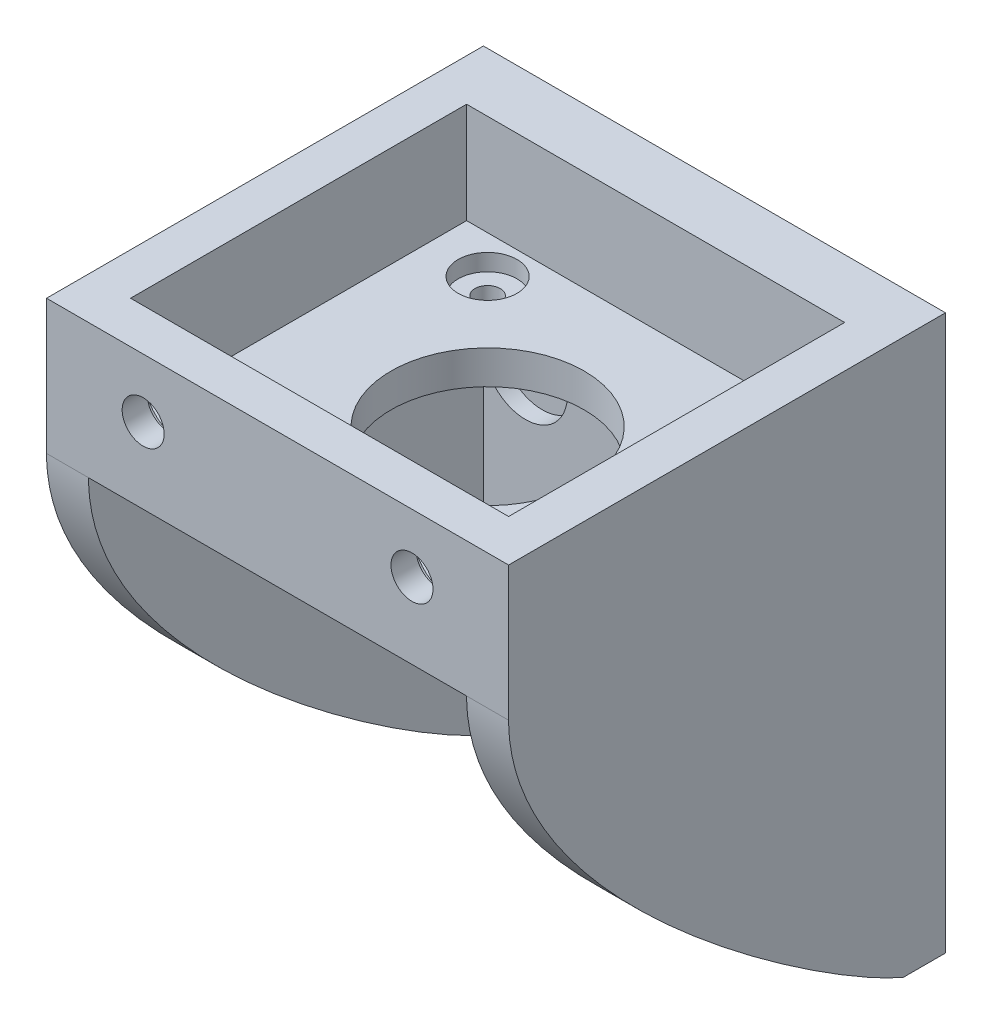
SolidWorks part; units mm, degrees
ref_plane "Front" through (0, 0, 0) normal (0, 0, 1) x (1, 0, 0)
ref_plane "Top" through (0, 0, 0) normal (0, 1, 0) x (1, 0, 0)
ref_plane "Right" through (0, 0, 0) normal (1, 0, 0) x (0, 0, -1)
sketch "Sketch1" plane through (0, 0, 0) normal (0, 0, 1) x (1, 0, 0)
  line L0 (0, 10.6846) -> (0, -12.6556) construction
  line L1 (-27.5, 25) -> (27.5, 25)
  line L2 (-27.5, 25) -> (-27.5, -25)
  line L3 (-27.5, -25) -> (27.5, -25)
  line L4 (27.5, 25) -> (27.5, -25)
  line L5 (-27.5, 25) -> (27.5, -25) construction
  line L6 (-27.5, -25) -> (27.5, 25) construction
  line L7 (-31.8369, 0) -> (16.1153, 0) construction
  circle A0 centre (-17.5, -15) radius 2.5
  circle A1 centre (17.5, -15) radius 2.5
  circle A2 centre (-17.5, 15) radius 2.5
  circle A3 centre (17.5, 15) radius 2.5
  point P0 (0, 0)
  dimension "D3" = 5
  dimension "D1" = 50
  dimension "D2" = 55
  dimension "D4" = 10
  dimension "D5" = 10
extrude "Boss-Extrude1" add sketch "Sketch1" along normal blind 5
sketch "Sketch2" plane through (0, 0, 5) normal (0, 0, 1) x (1, 0, 0)
  line L0 (-30.4627, 0) -> (10.8931, 0) construction
  circle A0 centre (-17.5, -15) radius 5
  circle A1 centre (17.5, -15) radius 5
  circle A3 centre (-17.5, 15) radius 5
  circle A4 centre (17.5, 15) radius 5
  dimension "D1" = 10
extrude "Cut-Extrude1" cut sketch "Sketch2" against normal blind 2
sketch "Sketch3" plane through (0, 25, 0) normal (0, 1, 0) x (1, 0, 0)
  line L1 (-27.5, 0) -> (27.5, 0)
  line L2 (-27.5, 0) -> (-27.5, -52)
  line L3 (-27.5, -52) -> (27.5, -52)
  line L4 (27.5, 0) -> (27.5, -52)
  dimension "D1" = 52
extrude "Boss-Extrude2" add sketch "Sketch3" along normal blind 16
sketch "Sketch4" plane through (0, 25, 0) normal (0, -1, 0) x (-1, 0, 0)
  line L0 (27.5, -5) -> (-27.5, -5) construction
  circle A0 centre (0, -27) radius 11.5
  circle A2 centre (15.5, -42.5) radius 1.5
  circle A3 centre (-15.5, -42.5) radius 1.5
  circle A4 centre (-15.5, -11.5) radius 1.5
  circle A5 centre (15.5, -11.5) radius 1.5
  dimension "D1" = 22
  dimension "D2" = 23
  dimension "D5" = 4
extrude "Cut-Extrude2" cut sketch "Sketch4" against normal through all
sketch "Sketch5" plane through (-27.5, 0, 0) normal (-1, 0, 0) x (0, 0, 1)
  line L0 (5, -25) -> (5, 25)
  line L1 (5, 25) -> (52, 25)
  spline S0 degree 3 poles (52, 25) (52, 4.233) (15.2666, -20.7199) (5, -25) knots 0 0 0 0 0.911488 0.911488 0.911488 0.911488
extrude "Boss-Extrude3" add sketch "Sketch5" against normal blind 5
mirror "Mirror1" about plane through (0, 0, 0) normal (1, 0, 0) of "Boss-Extrude3"
sketch "Sketch6" plane through (0, 41, 0) normal (0, 1, 0) x (1, 0, 0)
  line L1 (-22.5, -7) -> (22.5, -7)
  line L2 (-22.5, -7) -> (-22.5, -47)
  line L3 (-22.5, -47) -> (22.5, -47)
  line L4 (22.5, -7) -> (22.5, -47)
  line L5 (-22.5, -7) -> (22.5, -47) construction
  line L6 (-22.5, -47) -> (22.5, -7) construction
  point P0 (0, -27)
  dimension "D1" = 40
  dimension "D2" = 45
extrude "Cut-Extrude3" cut sketch "Sketch6" against normal blind 12
sketch "Sketch7" plane through (0, 29, 0) normal (0, 1, 0) x (1, 0, 0)
  circle A0 centre (-15.5, -11.5) radius 3.5
  circle A1 centre (15.5, -11.5) radius 3.5
  circle A2 centre (15.5, -42.5) radius 3.5
  circle A3 centre (-15.5, -42.5) radius 3.5
  dimension "D1" = 4
extrude "Cut-Extrude4" cut sketch "Sketch7" against normal blind 2
sketch "Sketch8" plane through (0, 0, 52) normal (0, 0, 1) x (1, 0, 0)
  line L0 (-27.5, 41) -> (27.5, 41) construction
  line L1 (27.5, 41) -> (27.5, 25) construction
  line L2 (0, 40.3655) -> (0, 13.7518) construction
  circle A0 centre (16, 34) radius 2.5
  circle A1 centre (-16, 34) radius 2.5
  dimension "D1" = 5
  dimension "D2" = 7
  dimension "D3" = 11.5
extrude "Cut-Extrude5" cut sketch "Sketch8" against normal blind 5
sketch "Sketch10" plane through (0, 0, 47) normal (0, 0, -1) x (-1, 0, 0)
  line L0 (-27.5, 41) -> (27.5, 41) construction
  line L1 (-27.5, -25) -> (-27.5, 41) construction
  line L2 (0, 40.623) -> (0, 10.3177) construction
  circle A0 centre (-16, 34) radius 5
  circle A1 centre (16, 34) radius 5
  dimension "D1" = 7
  dimension "D3" = 10
  dimension "D2" = 11.5
extrude "Cut-Extrude6" cut sketch "Sketch10" against normal blind 2
